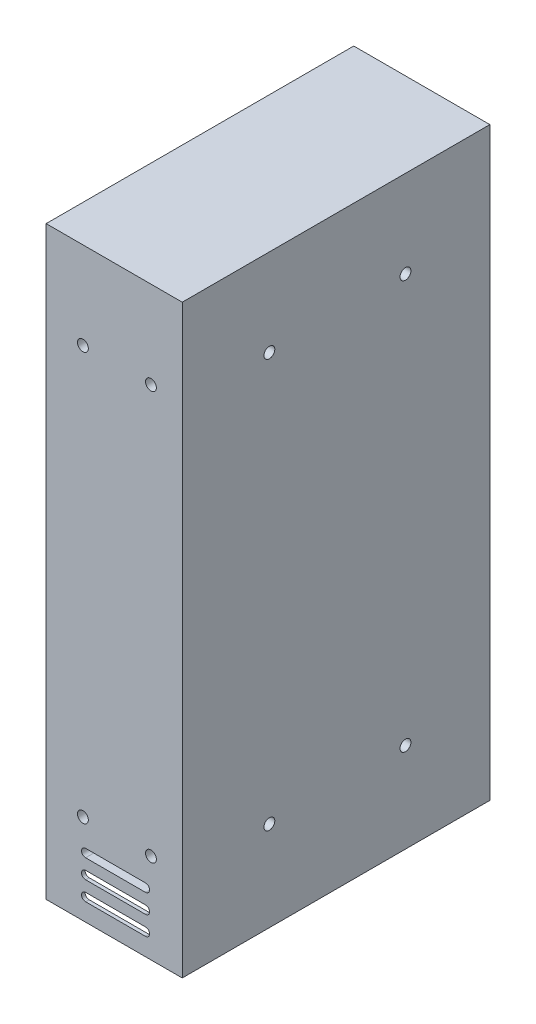
SolidWorks part; units mm, degrees
ref_plane "Plano frontal" through (0, 0, 0) normal (0, 0, 1) x (1, 0, 0)
ref_plane "Plano superior" through (0, 0, 0) normal (0, 1, 0) x (1, 0, 0)
ref_plane "Plano direito" through (0, 0, 0) normal (1, 0, 0) x (0, 0, -1)
sketch "Esboço1" plane through (0, 0, 0) normal (0, 0, 1) x (1, 0, 0)
  line L1 (-25, 107.5) -> (25, 107.5)
  line L2 (-25, 107.5) -> (-25, -107.5)
  line L3 (-25, -107.5) -> (25, -107.5)
  line L4 (25, 107.5) -> (25, -107.5)
  line L5 (-25, 107.5) -> (25, -107.5) construction
  line L6 (-25, -107.5) -> (25, 107.5) construction
  point P0 (0, 0)
  dimension "D1" = 50
  dimension "D2" = 215
extrude "Ressalto-extrusão1" add sketch "Esboço1" along normal blind 113
sketch "Esboço2" plane through (0, 0, 0) normal (0, 0, -1) x (-1, 0, 0)
  line L0 (-11.5, -99.5) -> (10.5, -99.5) construction
  line L1 (-11.5, -98) -> (10.5, -98)
  line L2 (-11.5, -101) -> (10.5, -101)
  line L3 (-25, -107.5) -> (-25, 107.5) construction
  line L4 (25, -107.5) -> (-25, -107.5) construction
  line L5 (-11.5, -92.5) -> (10.5, -92.5) construction
  line L6 (-11.5, -91) -> (10.5, -91)
  line L7 (-11.5, -94) -> (10.5, -94)
  line L8 (-11.5, -85.5) -> (10.5, -85.5) construction
  line L9 (-11.5, -84) -> (10.5, -84)
  line L10 (-11.5, -87) -> (10.5, -87)
  arc A0 (-11.5, -98) -> (-11.5, -101) centre (-11.5, -99.5) ccw
  arc A1 (10.5, -101) -> (10.5, -98) centre (10.5, -99.5) ccw
  arc A2 (-11.5, -91) -> (-11.5, -94) centre (-11.5, -92.5) ccw
  arc A3 (10.5, -94) -> (10.5, -91) centre (10.5, -92.5) ccw
  arc A4 (-11.5, -84) -> (-11.5, -87) centre (-11.5, -85.5) ccw
  arc A5 (10.5, -87) -> (10.5, -84) centre (10.5, -85.5) ccw
  point P2 (-0.5, -99.5)
  point P15 (-0.5, -92.5)
  point P22 (-0.5, -85.5)
  dimension "D1" = 1.5
  dimension "D2" = 22
  dimension "D3" = 13.5
  dimension "D4" = 6.5
  dimension "D5" = 3
extrude "Corte-extrusão1" cut sketch "Esboço2" against normal up to surface (113 mm away) up to face at (0, 0, 113)
sketch "Esboço3" plane through (-25, 0, 0) normal (-1, 0, 0) x (0, 0, 1)
  line L0 (111.7, -107.5) -> (111.7, 107.5)
  line L1 (1.3, 107.5) -> (1.3, -107.5)
  line L2 (0, -87.5) -> (113, -87.5)
  line L4 (0, 107.5) -> (0, -107.5)
  line L5 (0, -107.5) -> (113, -107.5)
  line L6 (113, -107.5) -> (113, 107.5)
  line L7 (113, 107.5) -> (0, 107.5)
  line L8 (0, 107.5) -> (0, -107.5)
  line L9 (0, -107.5) -> (113, -107.5)
  line L10 (113, -107.5) -> (113, 107.5)
  line L11 (113, 107.5) -> (0, 107.5)
  line M6 (0, -107.5) -> (113, -107.5)
  dimension "D1" = 0
  dimension "D2" = 1.3
  dimension "D3" = 20
extrude "Corte-extrusão2" cut sketch "Esboço3" against normal blind 43 contours L2 L1 L0 M6
sketch "Esboço4" plane through (0, 0, 113) normal (0, 0, 1) x (1, 0, 0)
  line L0 (-11.5, -74.5) -> (13.5, -74.5) construction
  line L1 (25, -107.5) -> (25, 107.5) construction
  line L2 (-25, -107.5) -> (25, -107.5) construction
  circle A0 centre (13.5, -74.5) radius 2
  circle A1 centre (-11.5, -74.5) radius 2
  circle A2 centre (13.5, 75.5) radius 2
  dimension "D1" = 4
  dimension "D2" = 4
  dimension "D3" = 25
  dimension "D4" = 11.5
  dimension "D5" = 33
  dimension "D6" = 150
extrude "Corte-extrusão3" cut sketch "Esboço4" against normal up to surface (113 mm away) contours A0 | A2 up to face at (0.5, -99.5, 0)
sketch "Esboço5" plane through (0, 0, 113) normal (0, 0, 1) x (1, 0, 0)
  circle A0 centre (-11.5, 75.5) radius 2
  circle A1 centre (-11.5, -74.5) radius 2
  circle A3 centre (13.5, -74.5) radius 2 construction
  dimension "D1" = 4
  dimension "D2" = 25
  dimension "D3" = 150
extrude "Corte-extrusão4" cut sketch "Esboço5" against normal blind 10
sketch "Esboço6" plane through (25, 0, 0) normal (1, 0, 0) x (0, 0, -1)
  line L0 (-113, -107.5) -> (0, -107.5) construction
  line L1 (-81, -74.5) -> (-31, -74.5) construction
  line L2 (-113, -107.5) -> (0, -107.5)
  line L4 (0, -107.5) -> (0, 107.5) construction
  circle A0 centre (-31, -74.5) radius 2
  circle A1 centre (-81, -74.5) radius 2
  circle A2 centre (-31, 75.5) radius 2
  circle A3 centre (-81, 75.5) radius 2
  point P7 (-56.5, -107.5)
  dimension "D1" = 4
  dimension "D2" = 50
  dimension "D3" = 33
  dimension "D4" = 150
  dimension "D5" = 31
extrude "Corte-extrusão5" cut sketch "Esboço6" against normal blind 10
